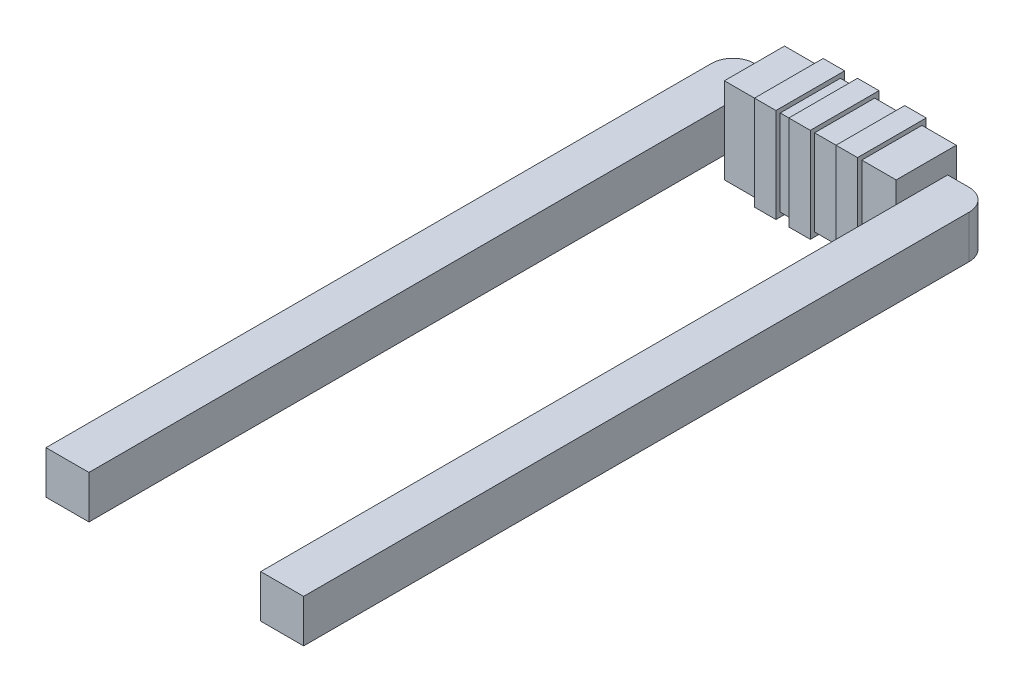
SolidWorks part; units mm, degrees
ref_plane "Front Plane" through (0, 0, 0) normal (0, 0, 1) x (1, 0, 0)
ref_plane "Top Plane" through (0, 0, 0) normal (0, 1, 0) x (1, 0, 0)
ref_plane "Right Plane" through (0, 0, 0) normal (1, 0, 0) x (0, 0, -1)
sketch "Sketch1" plane through (0, 0, 0) normal (0, 1, 0) x (1, 0, 0)
  line L0 (-1.4596, 0) -> (-1.4596, 15.5)
  line L1 (-0.9596, 16) -> (4.0404, 16)
  line L2 (4.5404, 15.5) -> (4.5404, 0)
  line L3 (4.5404, 0) -> (3.5404, 0)
  line L4 (3.5404, 0) -> (3.5404, 15)
  line L5 (3.5404, 15) -> (-0.4596, 15)
  line L6 (-0.4596, 15) -> (-0.4596, 0)
  line L7 (-0.4596, 0) -> (-1.4596, 0)
  arc A0 (-0.9596, 16) -> (-1.4596, 15.5) centre (-0.9596, 15.5) ccw
  arc A1 (4.5404, 15.5) -> (4.0404, 16) centre (4.0404, 15.5) ccw
  dimension "D7" = 1
  dimension "D8" = 1
  dimension "D1" = 15
  dimension "D2" = 15
  dimension "D3" = 4
  dimension "D4" = 1
  dimension "D5" = 1
  dimension "D6" = 1
extrude "Boss-Extrude1" add sketch "Sketch1" along normal blind 1
sketch "Sketch2" plane through (0, 1, 0) normal (0, 1, 0) x (1, 0, 0)
  line L0 (-1.4596, 15.5) -> (-1.4596, 0) construction
  line L1 (4.0404, 17.5) -> (14.0404, 17.5)
  line L2 (4.0404, 17.5) -> (4.0404, 13.5)
  line L3 (4.0404, 13.5) -> (14.0404, 13.5)
  line L4 (14.0404, 17.5) -> (14.0404, 13.5)
  line L5 (-1.4596, 0) -> (-0.4596, 0) construction
  line L6 (3.5404, 15) -> (3.5404, 0) construction
  dimension "D1" = 10
  dimension "D2" = 5.5
  dimension "D3" = 4
  dimension "D4" = 13.5
  dimension "D5" = 10.5
sketch "Sketch3" plane through (0, 1, 0) normal (0, 1, 0) x (1, 0, 0)
  line L0 (-0.4596, 15) -> (3.5404, 15) construction
  line L1 (-0.4596, 16.2) -> (3.5404, 16.2)
  line L2 (-0.4596, 16.2) -> (-0.4596, 14.8)
  line L3 (-0.4596, 14.8) -> (3.5404, 14.8)
  line L4 (3.5404, 16.2) -> (3.5404, 14.8)
  line L5 (4.0404, 16) -> (-0.9596, 16) construction
  line L6 (-1.4596, 15.5) -> (-1.4596, 0) construction
  line L7 (4.5404, 0) -> (4.5404, 15.5) construction
  dimension "D1" = 0.2
  dimension "D2" = 0.2
  dimension "D3" = 1
  dimension "D4" = 1
  dimension "D5" = 4
extrude "Boss-Extrude2" add sketch "Sketch3" against normal mid plane 3 from offset 0
sketch "Sketch4" plane through (0, 2.5, 0) normal (0, 1, 0) x (1, 0, 0)
  line L1 (-0.4596, 16.2) -> (3.5404, 16.2)
  line L2 (-0.4596, 16.2) -> (-0.4596, 14.8)
  line L3 (-0.4596, 14.8) -> (3.5404, 14.8)
  line L4 (3.5404, 16.2) -> (3.5404, 14.8)
extrude "Cut-Extrude1" cut sketch "Sketch4" against normal blind 1
sketch "Sketch5" plane through (0, 1.5, 0) normal (0, 1, 0) x (1, 0, 0)
  line L0 (-0.4596, 16.2) -> (-0.4596, 14.8) construction
  line L1 (0.3404, 16.3) -> (0.8404, 16.3)
  line L2 (0.3404, 16.3) -> (0.3404, 14.7)
  line L3 (0.3404, 14.7) -> (0.8404, 14.7)
  line L4 (0.8404, 16.3) -> (0.8404, 14.7)
  line L5 (1.1404, 16.3) -> (1.6404, 16.3)
  line L6 (1.1404, 16.3) -> (1.1404, 14.7)
  line L7 (1.1404, 14.7) -> (1.6404, 14.7)
  line L8 (1.6404, 16.3) -> (1.6404, 14.7)
  line L9 (2.2404, 16.3) -> (2.7404, 16.3)
  line L10 (2.2404, 16.3) -> (2.2404, 14.7)
  line L11 (2.2404, 14.7) -> (2.7404, 14.7)
  line L12 (2.7404, 16.3) -> (2.7404, 14.7)
  line L14 (3.5404, 16.2) -> (-0.4596, 16.2) construction
  line L15 (-0.4596, 14.8) -> (3.5404, 14.8) construction
  dimension "D1" = 0.5
  dimension "D2" = 0.5
  dimension "D3" = 0.5
  dimension "D4" = 0.8
  dimension "D5" = 0.3
  dimension "D6" = 0.6
  dimension "D7" = 0.1
  dimension "D8" = 0.1
  dimension "D9" = 0.1
  dimension "D10" = 0.1
extrude "Boss-Extrude4" add sketch "Sketch5" against normal blind 2.1
sketch "Sketch6" plane through (0, 1.5, 0) normal (0, 1, 0) x (1, 0, 0)
  line L0 (1.6404, 16.3) -> (1.1404, 16.3) construction
  line L1 (0.3404, 16.3) -> (0.8404, 16.3)
  line L2 (0.3404, 16.3) -> (0.3404, 14.7)
  line L3 (0.3404, 14.7) -> (0.8404, 14.7)
  line L4 (0.8404, 16.3) -> (0.8404, 14.7)
  line L5 (1.1404, 16.3) -> (1.6404, 16.3)
  line L6 (1.1404, 16.3) -> (1.1404, 14.7)
  line L7 (1.1404, 14.7) -> (1.6404, 14.7)
  line L8 (1.6404, 16.3) -> (1.6404, 14.7)
  line L9 (2.7404, 16.3) -> (2.2404, 16.3) construction
  line L10 (2.2404, 16.3) -> (2.7404, 16.3)
  line L11 (2.2404, 16.3) -> (2.2404, 14.7)
  line L12 (2.2404, 14.7) -> (2.7404, 14.7)
  line L13 (2.7404, 16.3) -> (2.7404, 14.7)
extrude "Boss-Extrude5" add sketch "Sketch6" along normal blind 0.1
